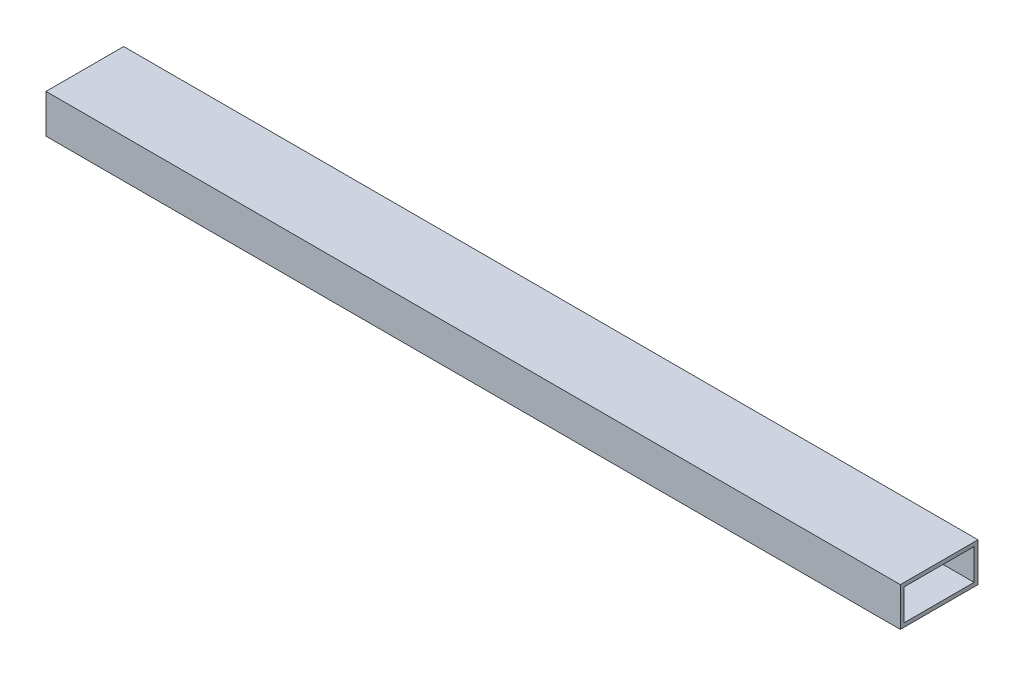
SolidWorks part; units mm, degrees
ref_plane "Front Plane" through (0, 0, 0) normal (0, 0, 1) x (1, 0, 0)
ref_plane "Top Plane" through (0, 0, 0) normal (0, 1, 0) x (1, 0, 0)
ref_plane "Right Plane" through (0, 0, 0) normal (1, 0, 0) x (0, 0, -1)
sketch "Sketch1" plane through (0, 0, 0) normal (0, 1, 0) x (1, 0, 0)
  line L1 (279.4, -25.4) -> (-279.4, -25.4)
  line L2 (279.4, -25.4) -> (279.4, 25.4)
  line L3 (279.4, 25.4) -> (-279.4, 25.4)
  line L4 (-279.4, -25.4) -> (-279.4, 25.4)
  line L5 (279.4, -25.4) -> (-279.4, 25.4) construction
  line L6 (279.4, 25.4) -> (-279.4, -25.4) construction
  point P0 (0, 0)
  dimension "D1" = 558.8
  dimension "D2" = 50.8
extrude "Boss-Extrude1" add sketch "Sketch1" along normal blind 25.4
sketch "Sketch2" plane through (279.4, 0, 0) normal (1, 0, 0) x (0, 0, -1)
  line L0 (-25.4, 25.4) -> (25.4, 25.4) construction
  line L1 (22.86, 2.54) -> (-22.86, 2.54)
  line L2 (22.86, 2.54) -> (22.86, 22.86)
  line L3 (22.86, 22.86) -> (-22.86, 22.86)
  line L4 (-22.86, 2.54) -> (-22.86, 22.86)
  line L5 (22.86, 2.54) -> (-22.86, 22.86) construction
  line L6 (22.86, 22.86) -> (-22.86, 2.54) construction
  line L7 (-25.4, 25.4) -> (-25.4, 0) construction
  line L8 (25.4, 25.4) -> (25.4, 0) construction
  line L9 (-25.4, 0) -> (25.4, 0) construction
  point P0 (0, 12.7)
  dimension "D1" = 2.54
  dimension "D2" = 2.54
  dimension "D3" = 2.54
  dimension "D4" = 2.54
extrude "Cut-Extrude1" cut sketch "Sketch2" against normal blind 558.8
